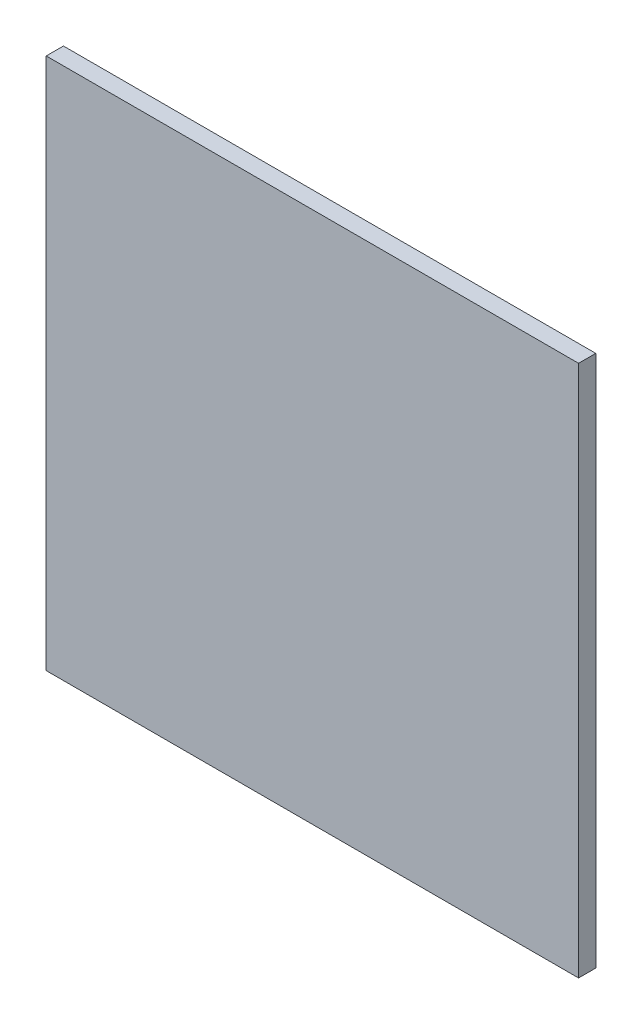
SolidWorks part; units mm, degrees
ref_plane "Front Plane" through (0, 0, 0) normal (0, 0, 1) x (1, 0, 0)
ref_plane "Top Plane" through (0, 0, 0) normal (0, 1, 0) x (1, 0, 0)
ref_plane "Right Plane" through (0, 0, 0) normal (1, 0, 0) x (0, 0, -1)
sketch "Sketch1" plane through (0, 0, 0) normal (0, 0, 1) x (1, 0, 0)
  line L1 (0, 0) -> (368.3, 0)
  line L2 (0, 0) -> (0, 368.3)
  line L3 (0, 368.3) -> (368.3, 368.3)
  line L4 (368.3, 0) -> (368.3, 368.3)
  dimension "D1" = 368.3
  dimension "D2" = 368.3
extrude "Boss-Extrude1" add sketch "Sketch1" along normal blind 11.9062
